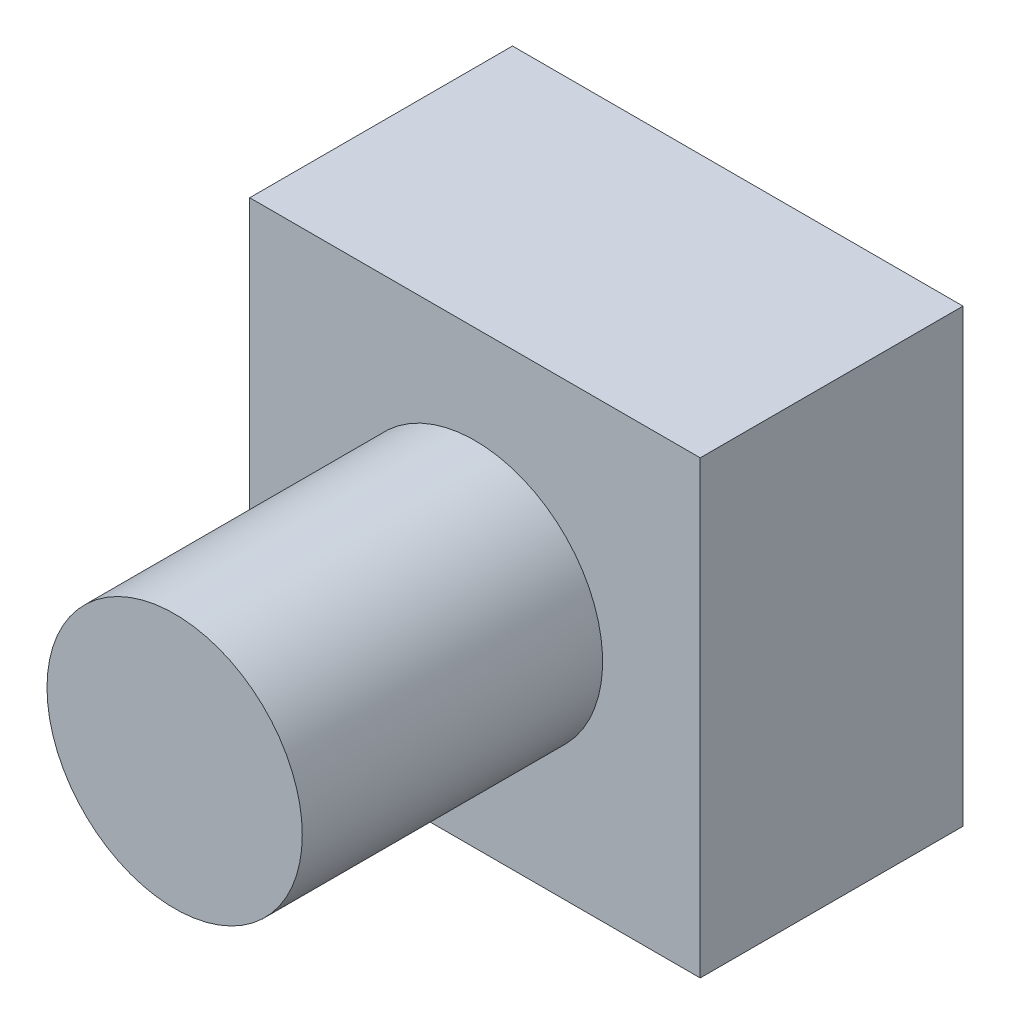
SolidWorks part; units mm, degrees
material "Acrylic (Medium-high impact)"
ref_plane "Front Plane" through (0, 0, 0) normal (0, 0, 1) x (1, 0, 0)
ref_plane "Top Plane" through (0, 0, 0) normal (0, 1, 0) x (1, 0, 0)
ref_plane "Right Plane" through (0, 0, 0) normal (1, 0, 0) x (0, 0, -1)
sketch "Sketch1" plane through (0, 0, 0) normal (0, 0, 1) x (1, 0, 0)
  line L1 (0, 0) -> (6, 0)
  line L2 (0, 0) -> (0, 6)
  line L3 (0, 6) -> (6, 6)
  line L4 (6, 0) -> (6, 6)
  dimension "D1" = 6
  dimension "D2" = 6
extrude "Boss-Extrude1" add sketch "Sketch1" along normal blind 3.5
sketch "Sketch2" plane through (0, 0, 3.5) normal (0, 0, 1) x (1, 0, 0)
  line L1 (6, 0) -> (6, 6) construction
  line L2 (6, 6) -> (0, 6) construction
  circle A0 centre (3, 3) radius 1.7
  dimension "D1" = 3.4
  dimension "D2" = 3
  dimension "D3" = 3
extrude "Boss-Extrude2" add sketch "Sketch2" along normal blind 4
